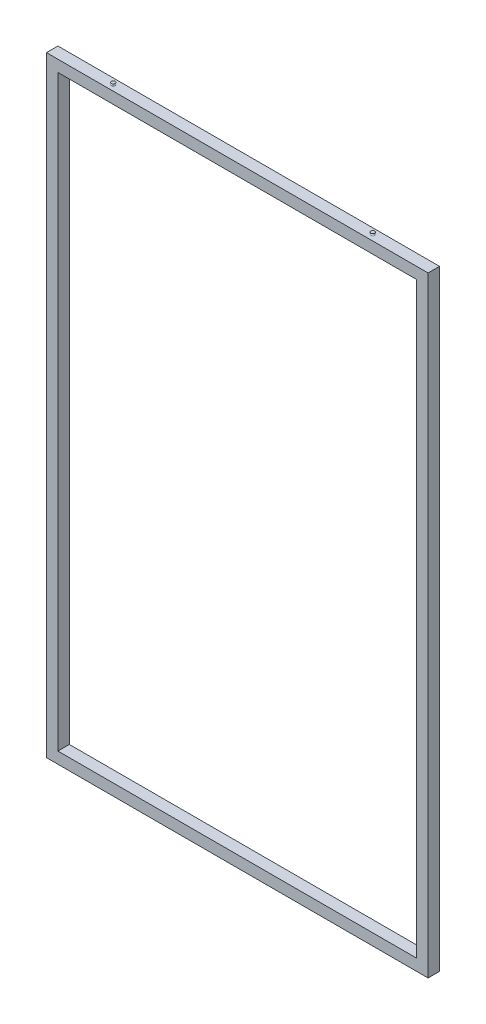
SolidWorks part; units mm, degrees
ref_plane "Front Plane" through (0, 0, 0) normal (0, 0, 1) x (1, 0, 0)
ref_plane "Top Plane" through (0, 0, 0) normal (0, 1, 0) x (1, 0, 0)
ref_plane "Right Plane" through (0, 0, 0) normal (1, 0, 0) x (0, 0, -1)
sketch "Sketch1" plane through (0, 0, 0) normal (0, 0, 1) x (1, 0, 0)
  line L0 (-470, 770) -> (470, 770)
  line L1 (-500, 800) -> (500, 800)
  line L2 (-500, 800) -> (-500, -800)
  line L3 (-500, -800) -> (500, -800)
  line L4 (500, 800) -> (500, -800)
  line L5 (-500, 800) -> (500, -800) construction
  line L6 (-500, -800) -> (500, 800) construction
  line L7 (470, 770) -> (470, -770)
  line L8 (-470, -770) -> (470, -770)
  line L9 (-470, 770) -> (-470, -770)
  point P0 (0, 0)
  dimension "D1" = 1600
  dimension "D2" = 1000
  dimension "D3" = 30
extrude "Boss-Extrude1" add sketch "Sketch1" along normal mid plane 30
sketch "Sketch2" plane through (0, 0, 0) normal (1, 0, 0) x (0, 0, -1)
  line L3 (-15, 800) -> (15, 800) construction
  line L4 (-15, 770) -> (15, 770) construction
  line L5 (-15, 800) -> (15, 800) construction
  line L6 (-15, 770) -> (15, 770) construction
  line L7 (-15, 800) -> (-15, 770) construction
  line L8 (15, 800) -> (15, 770) construction
  line L10 (13, 798) -> (13, 772)
  line L11 (-13, 772) -> (13, 772)
  line L12 (-13, 798) -> (-13, 772)
  line L13 (-13, 798) -> (13, 798)
  dimension "D1" = 2
sketch "Sketch4" plane through (0, 0, 0) normal (0, 0, 1) x (1, 0, 0)
  line L0 (-485, 785) -> (-485, -785)
  line L1 (-485, -785) -> (485, -785)
  line L2 (485, -785) -> (485, 785)
  line L3 (485, 785) -> (-485, 785)
  line L4 (500, -800) -> (500, 800)
  line L5 (500, 800) -> (-500, 800)
  line L6 (-500, 800) -> (-500, -800)
  line L7 (-500, -800) -> (500, -800)
  line L8 (500, -800) -> (500, 800)
  line L9 (500, 800) -> (-500, 800)
  line L10 (-500, 800) -> (-500, -800)
  line L11 (-500, -800) -> (500, -800)
  dimension "D1" = 0
  dimension "D2" = 15
sweep "Cut-Sweep1" cut profiles "Sketch2" path "Sketch4"
sketch "Sketch5" plane through (0, 800, 0) normal (0, 1, 0) x (1, 0, 0)
  line L0 (0, 18.3123) -> (0, -18.3123) construction
  line L6 (500, 15) -> (-500, 15)
  line L7 (-500, 15) -> (-500, -15)
  line L8 (-500, -15) -> (500, -15)
  line L9 (500, -15) -> (500, 15)
  line L10 (500, 15) -> (-500, 15)
  line L11 (-500, 15) -> (-500, -15)
  line L12 (-500, -15) -> (500, -15)
  line L13 (500, -15) -> (500, 15)
  circle A0 centre (-340, 0) radius 15 construction
  circle A1 centre (-340, 0) radius 7
  point P4 (0, 0)
  dimension "D1" = 340
  dimension "D2" = 0
  dimension "D3" = 8
ref_plane "Plane1" through (0, 806.8, 0) normal (0, 1, 0) x (1, 0, 0)
sketch "Sketch6" plane through (0, 806.8, 0) normal (0, 1, 0) x (1, 0, 0)
  circle A2 centre (-340, 0) radius 7 construction
  circle A3 centre (-340, 0) radius 7
sketch "Sketch7" plane through (0, 0, 0) normal (0, 0, 1) x (1, 0, 0)
  line L5 (-340, 800) -> (-340, 805)
  line L6 (-345, 805) -> (-340, 805)
  line L7 (-345, 800) -> (-340, 800)
  line L8 (-340, 795.1043) -> (-340, 811.1427) construction
  arc A0 (-345, 800) -> (-345, 805) centre (-345, 802.5) ccw
  point P12 (-340, 802.5)
  dimension "D1" = 2.5
  dimension "D2" = 5
revolve "Revolve1" add sketch "Sketch7" angle 360 about L8
mirror "Mirror1" about plane through (0, 0, 0) normal (1, 0, 0) of "Revolve1"
sketch "Sketch8" plane through (0, 805, 0) normal (0, 1, 0) x (1, 0, 0)
  circle A1 centre (340, 0) radius 5
  circle A2 centre (340, 0) radius 5
  point P0 (335, 0)
  dimension "D1" = 0
sketch "Sketch9" plane through (0, 0, 15) normal (0, 0, 1) x (1, 0, 0)
  line L0 (345, 805) -> (335, 805) construction
  line L1 (345, 805) -> (335, 805)
  point P2 (340, 805)
ref_plane "Plane2" through (340, 805, 15) normal (1, 0, 0) x (0, 0, -1)
ref_plane "Plane3" through (500, -800, 15) normal (0, 0, -1) x (-1, 0, 0)
